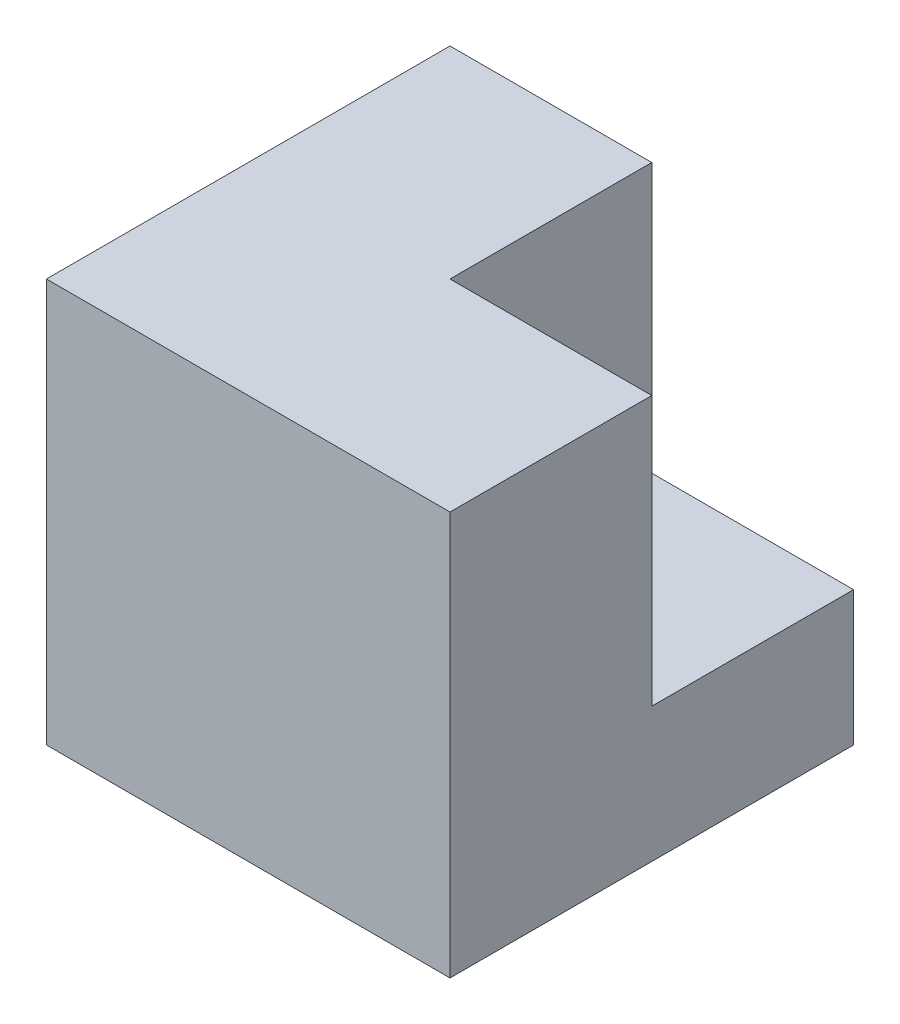
SolidWorks part; units mm, degrees
ref_plane "Front Plane" through (0, 0, 0) normal (0, 0, 1) x (1, 0, 0)
ref_plane "Top Plane" through (0, 0, 0) normal (0, 1, 0) x (1, 0, 0)
ref_plane "Right Plane" through (0, 0, 0) normal (1, 0, 0) x (0, 0, -1)
sketch "Sketch1" plane through (0, 0, 0) normal (0, 0, 1) x (1, 0, 0)
  line L1 (0, 0) -> (76.2, 0)
  line L2 (0, 0) -> (0, 76.2)
  line L3 (0, 76.2) -> (76.2, 76.2)
  line L4 (76.2, 0) -> (76.2, 76.2)
  dimension "D1" = 76.2
extrude "Boss-Extrude1" add sketch "Sketch1" along normal blind 76.2
sketch "Sketch2" plane through (76.2, 0, 0) normal (1, 0, 0) x (0, 0, -1)
  line L0 (-76.2, 0) -> (0, 0) construction
  line L1 (0, 76.2) -> (-38.1, 76.2)
  line L2 (0, 76.2) -> (0, 25.4)
  line L3 (0, 25.4) -> (-38.1, 25.4)
  line L4 (-38.1, 76.2) -> (-38.1, 25.4)
  dimension "D1" = 25.4
  dimension "D2" = 38.1
extrude "Cut-Extrude1" cut sketch "Sketch2" against normal blind 38.1
